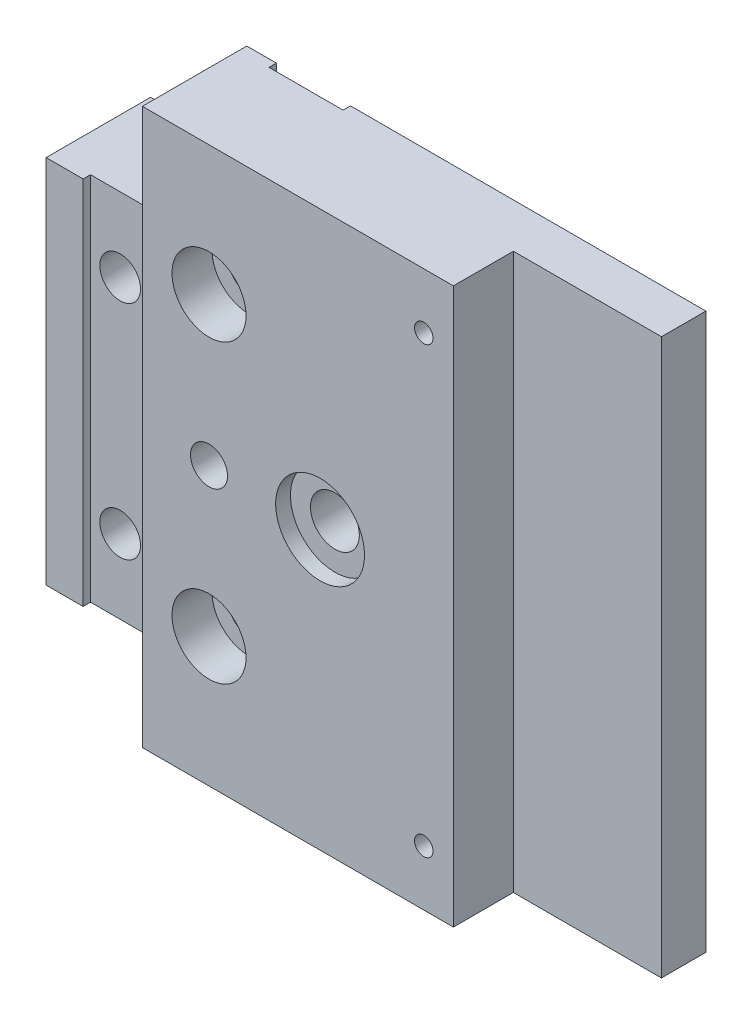
SolidWorks part; units mm, degrees
ref_plane "前视基准面" through (0, 0, 0) normal (0, 0, 1) x (1, 0, 0)
ref_plane "上视基准面" through (0, 0, 0) normal (0, 1, 0) x (1, 0, 0)
ref_plane "右视基准面" through (0, 0, 0) normal (1, 0, 0) x (0, 0, -1)
sketch "草图1" plane through (0, 0, 0) normal (0, 0, 1) x (1, 0, 0)
  line L1 (0, 0) -> (20, 0)
  line L2 (0, 0) -> (0, 75)
  line L3 (0, 75) -> (20, 75)
  line L4 (20, 0) -> (20, 75)
  dimension "D1" = 20
  dimension "D2" = 75
extrude "凸台-拉伸1" add sketch "草图1" along normal blind 6
sketch "草图2" plane through (0, 0, 0) normal (-1, 0, 0) x (0, 0, 1)
  line L1 (0, 75) -> (6, 75)
  line L2 (0, 75) -> (0, 0)
  line L3 (0, 0) -> (6, 0)
  line L4 (6, 75) -> (6, 0)
extrude "凸台-拉伸2" add sketch "草图2" along normal blind 20
sketch "草图3" plane through (0, 0, 6) normal (0, 0, 1) x (1, 0, 0)
  line L0 (-20, 0) -> (20, 0) construction
  line L1 (-20, 75) -> (0, 75)
  line L2 (-20, 75) -> (-20, 0)
  line L3 (-20, 0) -> (0, 0)
  line L4 (0, 75) -> (0, 0)
  dimension "D1" = 20
extrude "凸台-拉伸3" add sketch "草图3" along normal blind 8.1
sketch "草图4" plane through (-20, 0, 0) normal (-1, 0, 0) x (0, 0, 1)
  line L1 (14.1, 0) -> (0, 0)
  line L2 (14.1, 0) -> (14.1, 75)
  line L3 (14.1, 75) -> (0, 75)
  line L4 (0, 0) -> (0, 75)
extrude "凸台-拉伸4" add sketch "草图4" along normal blind 35
hole_wizard "M6 六角凹头螺钉的柱形沉头孔1" positions "草图7" profile "草图8" counterbore size "M6" standard "ISO" end condition through all
sketch "草图7" plane through (0, 0, 0) normal (0, 0, -1) x (-1, 0, 0)
  line L0 (55, 37.5) -> (-1.4171, 37.5) construction
  line L1 (55, 75) -> (55, 0) construction
  point P0 (18, 37.5)
  dimension "D1" = 37
sketch "草图8" plane through (-18, 37.5, 0) normal (1, 0, 0) x (0, 1, 0)
  line L0 (0, 0) -> (0, 14.1)
  line L1 (0, 14.1) -> (3.3, 14.1)
  line L3 (3.3, 14.1) -> (3.3, 6.4)
  line L4 (3.3, 6.4) -> (5.5, 6.4)
  line L5 (5.5, 6.4) -> (5.5, 0)
  line L7 (5.5, 0) -> (0, 0)
  line L11 (0, -6.35) -> (0, 107.95) construction
  dimension "通孔孔直径" = 6.6
  dimension "通孔孔深度" = 14.1
  dimension "柱形沉头孔直径" = 11
  dimension "柱形沉头孔深度" = 6.4
sketch "草图9" plane through (0, 0, 14.1) normal (0, 0, 1) x (1, 0, 0)
  circle A0 centre (-18, 37.5) radius 6
  dimension "D1" = 12
extrude "切除-拉伸1" cut sketch "草图9" against normal blind 2
hole_wizard "M3 螺纹孔1" positions "草图10" profile "草图11" tap size "M3" standard "ISO"
sketch "草图10" plane through (0, 0, 14.1) normal (0, 0, 1) x (1, 0, 0)
  point P0 (-4, 7.5)
  point P3 (-4, 67.5)
sketch "草图11" plane through (-4, 7.5, 14.1) normal (1, 0, 0) x (0, -1, 0)
  line L0 (0, 0) -> (0, 10.8511)
  line L1 (0, 10.8511) -> (1.25, 10.1)
  line L2 (1.25, 10.1) -> (1.25, 0)
  line L5 (1.25, 0) -> (0, 0)
  line L10 (0, 10.8511) -> (-1.25, 10.1) construction
  line L11 (0, -6.35) -> (0, 107.95) construction
  dimension "螺纹孔钻头直径" = 2.5
  dimension "螺纹孔钻头深度" = 10.1
  dimension "导头角度" = 118
cosmetic thread "孔螺蚊线3" parameters "D1"=6, "D2"=3
cosmetic thread "孔螺蚊线4" parameters "D1"=6, "D2"=3
sketch "草图15" plane through (0, 0, 14.1) normal (0, 0, 1) x (1, 0, 0)
  line L0 (-55, 0) -> (0, 0) construction
  line L1 (-42, 0) -> (-50, 0)
  line L2 (-42, 0) -> (-42, 75)
  line L3 (-42, 75) -> (-50, 75)
  line L4 (-50, 0) -> (-50, 75)
  line L5 (0, 75) -> (-55, 75) construction
  line L6 (-55, 0) -> (-55, 75) construction
  dimension "D1" = 5
  dimension "D2" = 8
extrude "切除-拉伸3" cut sketch "草图15" against normal blind 1
hole_wizard "M5 六角凹头螺钉的柱形沉头孔1" positions "草图16" profile "草图17" counterbore size "M5" standard "ISO" end condition through all
sketch "草图16" plane through (0, 0, 0) normal (0, 0, -1) x (-1, 0, 0)
  line L0 (55, 37.5) -> (34.1733, 37.5) construction
  line L1 (55, 75) -> (55, 0) construction
  point P0 (46, 52.5)
  point P2 (46, 22.5)
  dimension "D1" = 9
  dimension "D2" = 30
sketch "草图17" plane through (-46, 52.5, 0) normal (1, 0, 0) x (0, 1, 0)
  line L0 (0, 0) -> (0, 14.1)
  line L1 (0, 14.1) -> (2.75, 14.1)
  line L3 (2.75, 14.1) -> (2.75, 5.4)
  line L4 (2.75, 5.4) -> (5, 5.4)
  line L5 (5, 5.4) -> (5, 0)
  line L7 (5, 0) -> (0, 0)
  line L11 (0, -6.35) -> (0, 107.95) construction
  dimension "通孔孔直径" = 5.5
  dimension "通孔孔深度" = 14.1
  dimension "柱形沉头孔直径" = 10
  dimension "柱形沉头孔深度" = 5.4
hole_wizard "M6 螺纹孔1" positions "草图20" profile "草图21" tap size "M6" standard "ISO"
sketch "草图20" plane through (0, 0, 14.1) normal (0, 0, 1) x (1, 0, 0)
  line L0 (-42, 37.5) -> (0, 37.5) construction
  line L1 (-42, 0) -> (-42, 75) construction
  line L2 (0, 0) -> (0, 75) construction
  line L4 (-55, 0) -> (-55, 75) construction
  point P0 (-33, 37.5)
  dimension "D1" = 22
sketch "草图21" plane through (-33, 37.5, 14.1) normal (1, 0, 0) x (0, -1, 0)
  line L0 (0, 0) -> (0, 16.5022)
  line L1 (0, 16.5022) -> (2.5, 15)
  line L2 (2.5, 15) -> (2.5, 0)
  line L5 (2.5, 0) -> (0, 0)
  line L10 (0, 16.5022) -> (-2.5, 15) construction
  line L11 (0, -6.35) -> (0, 107.95) construction
  dimension "螺纹孔钻头直径" = 5
  dimension "螺纹孔钻头深度" = 15
  dimension "导头角度" = 118
cosmetic thread "孔螺蚊线5" parameters "D1"=12, "D2"=6
hole_wizard "M5 六角凹头螺钉的柱形沉头孔2" positions "草图22" profile "草图23" counterbore size "M5" standard "ISO" end condition through all
sketch "草图22" plane through (0, 0, 14.1) normal (0, 0, 1) x (1, 0, 0)
  line L0 (-42, 37.5) -> (10.2455, 37.5) construction
  line L1 (-42, 0) -> (-42, 75) construction
  line L3 (-55, 0) -> (-55, 75) construction
  point P0 (-33, 57.5)
  point P8 (-33, 17.5)
  dimension "D1" = 40
  dimension "D2" = 22
sketch "草图23" plane through (-33, 57.5, 14.1) normal (1, 0, 0) x (0, -1, 0)
  line L0 (0, 0) -> (0, 14.1)
  line L1 (0, 14.1) -> (2.75, 14.1)
  line L3 (2.75, 14.1) -> (2.75, 5.4)
  line L4 (2.75, 5.4) -> (5, 5.4)
  line L5 (5, 5.4) -> (5, 0)
  line L7 (5, 0) -> (0, 0)
  line L11 (0, -6.35) -> (0, 107.95) construction
  dimension "通孔孔直径" = 5.5
  dimension "通孔孔深度" = 14.1
  dimension "柱形沉头孔直径" = 10
  dimension "柱形沉头孔深度" = 5.4
sketch "草图24" plane through (0, 0, 0) normal (0, 0, -1) x (-1, 0, 0)
  line L0 (33, 57.5) -> (33, 17.5) construction
  line L1 (-20, 75) -> (55, 75) construction
  line L2 (28, 75) -> (38, 75)
  line L3 (28, 75) -> (28, 0)
  line L4 (28, 0) -> (38, 0)
  line L5 (38, 75) -> (38, 0)
  line L6 (55, 0) -> (-20, 0) construction
  dimension "D1" = 10
extrude "切除-拉伸4" cut sketch "草图24" against normal blind 1
sketch "草图25" plane through (0, 0, 14.1) normal (0, 0, 1) x (1, 0, 0)
  line L0 (-55, 37.5) -> (-25.1318, 37.5) construction
  line L1 (-55, 0) -> (-42, 0)
  line L2 (-55, 0) -> (-55, 12.5)
  line L3 (-55, 12.5) -> (-42, 12.5)
  line L4 (-42, 0) -> (-42, 12.5)
  line L5 (-55, 0) -> (-55, 75) construction
  line L6 (-55, 75) -> (-42, 75)
  line L7 (-55, 75) -> (-55, 62.5)
  line L8 (-55, 62.5) -> (-42, 62.5)
  line L9 (-42, 75) -> (-42, 62.5)
  dimension "D1" = 12.5
  dimension "D2" = 13
extrude "切除-拉伸5" cut sketch "草图25" against normal through all
